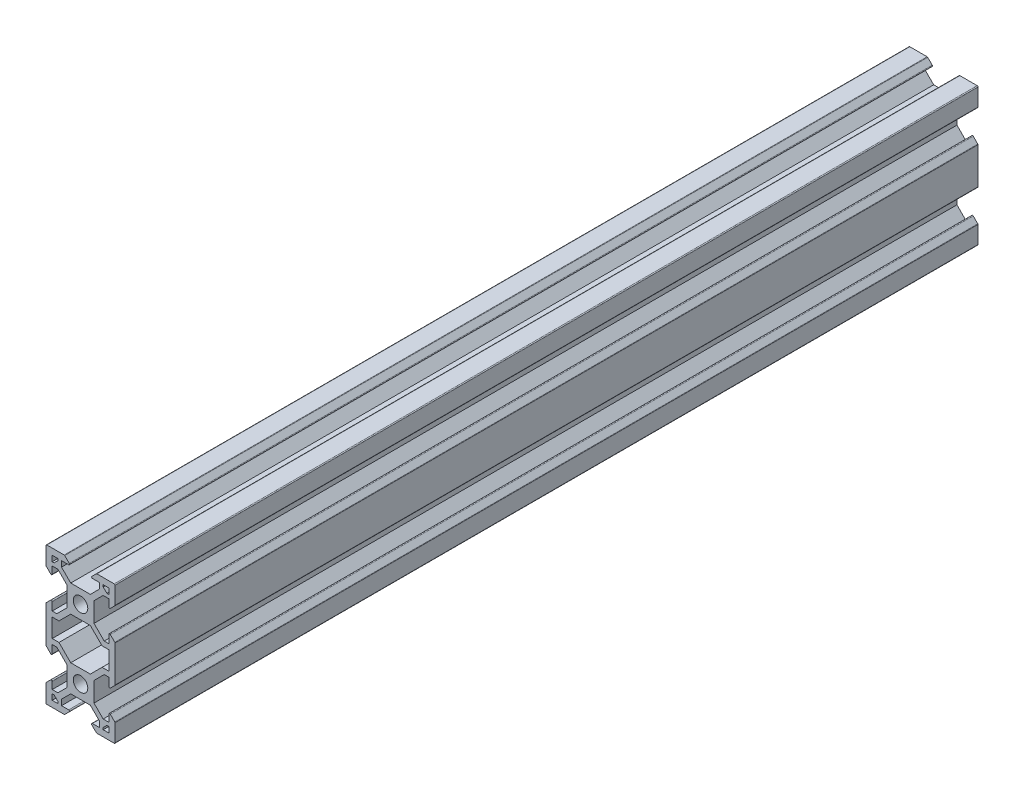
SolidWorks part; units mm, degrees
material "1060 Alloy"
ref_plane "Front Plane" through (0, 0, 0) normal (0, 0, 1) x (1, 0, 0)
ref_plane "Top Plane" through (0, 0, 0) normal (0, 1, 0) x (1, 0, 0)
ref_plane "Right Plane" through (0, 0, 0) normal (1, 0, 0) x (0, 0, -1)
sketch "Sketch1" plane through (0, 0, 0) normal (0, 0, 1) x (1, 0, 0)
  line L0 (8.2, -10) -> (10, -10)
  line L2 (10, -10) -> (10, -4.64)
  line L3 (10, -4.64) -> (8.2, -2.84)
  line L4 (8.2, -2.84) -> (8.2, -5.8007)
  line L5 (8.2, -5.8007) -> (6.8613, -5.8007)
  line L6 (6.8613, -5.8007) -> (3.9007, -2.84)
  line L7 (3.9007, -2.84) -> (3.9007, 2.84)
  line L8 (3.9007, 2.84) -> (6.56, 5.4993)
  line L9 (6.56, 5.4993) -> (8.2, 5.4993)
  line L10 (8.2, 5.4993) -> (8.2, 2.84)
  line L11 (8.2, 2.84) -> (10, 4.64)
  line L12 (10, 4.64) -> (10, 10)
  line L13 (10, 10) -> (4.64, 10)
  line L14 (4.64, 10) -> (2.84, 8.2)
  line L15 (2.84, 8.2) -> (5.4993, 8.2)
  line L16 (5.4993, 8.2) -> (5.4993, 6.56)
  line L17 (5.4993, 6.56) -> (2.84, 3.9007)
  line L18 (2.84, 3.9007) -> (-2.84, 3.9007)
  line L19 (-2.84, 3.9007) -> (-5.4993, 6.56)
  line L20 (-5.4993, 6.56) -> (-5.4993, 8.2)
  line L21 (-5.4993, 8.2) -> (-2.84, 8.2)
  line L22 (-2.84, 8.2) -> (-4.64, 10)
  line L23 (-4.64, 10) -> (-10, 10)
  line L24 (-10, 10) -> (-10, 4.64)
  line L25 (-10, 4.64) -> (-8.2, 2.84)
  line L26 (-8.2, 2.84) -> (-8.2, 5.4993)
  line L27 (-8.2, 5.4993) -> (-6.56, 5.4993)
  line L28 (-6.56, 5.4993) -> (-3.9007, 2.84)
  line L29 (-3.9007, 2.84) -> (-3.9007, -2.84)
  line L30 (-3.9007, -2.84) -> (-6.8613, -5.8007)
  line L31 (-6.8613, -5.8007) -> (-8.2, -5.8007)
  line L32 (-8.2, -5.8007) -> (-8.2, -2.84)
  line L33 (-8.2, -2.84) -> (-10, -4.64)
  line L34 (-10, -4.64) -> (-10, -10)
  line L64 (8.2, -7.3007) -> (8.2, -10)
  line L70 (-8.2, -10) -> (-8.2, -7.3007)
  line L71 (-8.2, -7.3007) -> (-6.24, -7.3007)
  line L72 (-6.24, -7.3007) -> (-2.84, -3.9007)
  line L73 (-2.84, -3.9007) -> (2.84, -3.9007)
  line L74 (2.84, -3.9007) -> (6.24, -7.3007)
  line L75 (6.24, -7.3007) -> (8.2, -7.3007)
  line L76 (-10, -10) -> (-8.2, -10)
  circle A0 centre (0, 0) radius 2.1
  point P46 (0, -3.9007)
  point P47 (0, 3.9007)
  point P49 (-3.9007, 0)
  point P50 (3.9007, 0)
  dimension "D1" = 4.2
  dimension "D8" = 1.8
  dimension "D2" = 20
  dimension "D3" = 20
  dimension "D4" = 5.68
  dimension "D5" = 90
  dimension "D6" = 10
  dimension "D7" = 10
  dimension "D9" = 1.8
  dimension "D10" = 1.8
  dimension "D11" = 1.5
  dimension "D12" = 1.5
  dimension "D13" = 1.64
  dimension "D14" = 1.5
  dimension "D15" = 1.96
extrude "Boss-Extrude2" add sketch "Sketch1" along normal blind 250
sketch "Sketch2" plane through (0, 0, 250) normal (0, 0, 1) x (1, 0, 0)
  line L0 (-8.2, 2.84) -> (-8.2, 5.4993) construction
  line L1 (-5.4993, 8.2) -> (-2.84, 8.2) construction
  line L2 (-8.2, 6.5693) -> (-8.2, 8.2)
  line L3 (-8.2, 8.2) -> (-6.5693, 8.2)
  line L4 (8.2, 5.4993) -> (8.2, 2.84) construction
  line L5 (8.2, 8.2) -> (8.2, 6.5693)
  line L6 (3.9007, 2.84) -> (6.56, 5.4993) construction
  line L7 (-5.4993, 6.56) -> (-5.4993, 8.2) construction
  line L8 (6.56, 5.4993) -> (8.2, 5.4993) construction
  line L11 (6.5693, 8.2) -> (6.5693, 6.56)
  line L12 (6.5693, 8.2) -> (6.5693, 7.63)
  line L16 (6.5693, 8.2) -> (8.2, 8.2)
  line L17 (-8.2, 6.5693) -> (-6.56, 6.5693)
  line L18 (-8.2, 6.5693) -> (-7.63, 6.5693)
  line L19 (-7.63, 6.5693) -> (-6.5693, 7.63)
  line L20 (6.5693, 7.63) -> (7.63, 6.5693)
  line L22 (7.63, 6.5693) -> (8.2, 6.5693)
  line L24 (-6.5693, 7.63) -> (-6.5693, 8.2)
  dimension "D5" = 1.5
  dimension "D1" = 1.07
  dimension "D3" = 1.07
  dimension "D2" = 1.07
  dimension "D4" = 1.07
extrude "Cut-Extrude1" cut sketch "Sketch2" against normal through all
fillet "Fillet1" radius 0.25 14 edges at (8.2, 2.84, 125) (-10, 4.64, 125) (-4.64, 10, 125) (4.64, 10, 125) (-10, -4.64, 125) (-10, 10, 125) (10, -4.64, 125) (10, 10, 125) (8.2, -2.84, 125) (-8.2, -2.84, 125) (-8.2, 2.84, 125) (10, 4.64, 125) (2.84, 8.2, 125) (-2.84, 8.2, 125)
ref_plane "Plane1" through (0, -10, 0) normal (0, -1, 0) x (-1, 0, 0)
mirror "Mirror1" about plane through (0, -10, 0) normal (0, -1, 0) of "Fillet1", "Boss-Extrude2"
mirror "Mirror2" about plane through (0, -10, 0) normal (0, -1, 0) of "Cut-Extrude1"
